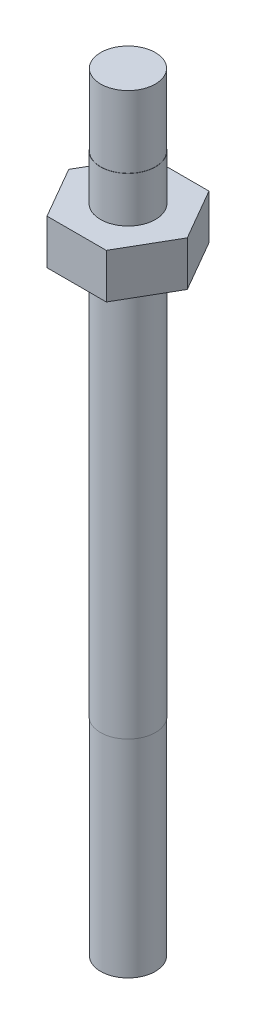
SolidWorks part; units mm, degrees
ref_plane "Front Plane" through (0, 0, 0) normal (0, 0, 1) x (1, 0, 0)
ref_plane "Top Plane" through (0, 0, 0) normal (0, 1, 0) x (1, 0, 0)
ref_plane "Right Plane" through (0, 0, 0) normal (1, 0, 0) x (0, 0, -1)
sketch "Sketch1" plane through (0, 0, 0) normal (0, 0, 1) x (1, 0, 0)
  line L0 (0, 0) -> (0, 90.7832) construction
  line L1 (0, 0) -> (1.6764, 0)
  line L2 (1.6764, 0) -> (1.6764, 12.7)
  line L3 (1.6764, 12.7) -> (1.6891, 12.7)
  line L4 (1.6891, 12.7) -> (1.6891, 37.211)
  line L5 (1.6891, 37.211) -> (3.1115, 37.211)
  line L6 (3.1115, 37.211) -> (3.1115, 39.9542)
  line L7 (3.1115, 39.9542) -> (1.6891, 39.9542)
  line L8 (1.6891, 39.9542) -> (1.6891, 42.7482)
  line L9 (1.6891, 42.7482) -> (1.6764, 42.7482)
  line L10 (1.6764, 42.7482) -> (1.6764, 47.1424)
  line L11 (1.6764, 47.1424) -> (0, 47.1424)
  line L12 (0, 47.1424) -> (0, 0)
  dimension "D1" = 3.1115
  dimension "D2" = 2.794
  dimension "D3" = 3.3528
  dimension "D4" = 3.3782
  dimension "D5" = 4.3942
  dimension "D6" = 37.211
  dimension "D7" = 12.7
  dimension "D8" = 2.7432
  dimension "D9" = 3.3782
  dimension "D10" = 3.3528
revolve "Revolve1" add sketch "Sketch1" angle 360 about L0
sketch "Sketch2" plane through (0, 39.9542, 0) normal (0, 1, 0) x (1, 0, 0)
  line L0 (0, 0) -> (3.6368, 0) construction
  line L1 (3.6368, 0) -> (1.8184, 3.1496)
  line L2 (1.8184, 3.1496) -> (-1.8184, 3.1496)
  line L3 (-1.8184, 3.1496) -> (-3.6368, 0)
  line L4 (-3.6368, 0) -> (-1.8184, -3.1496)
  line L5 (-1.8184, -3.1496) -> (1.8184, -3.1496)
  line L6 (1.8184, -3.1496) -> (3.6368, 0)
  circle A0 centre (0, 0) radius 3.1496 construction
  dimension "D1" = 6.2992
extrude "Boss-Extrude1" add sketch "Sketch2" against normal up to surface (2.7432 mm away) up to face at (0, 37.211, -3.1115)
